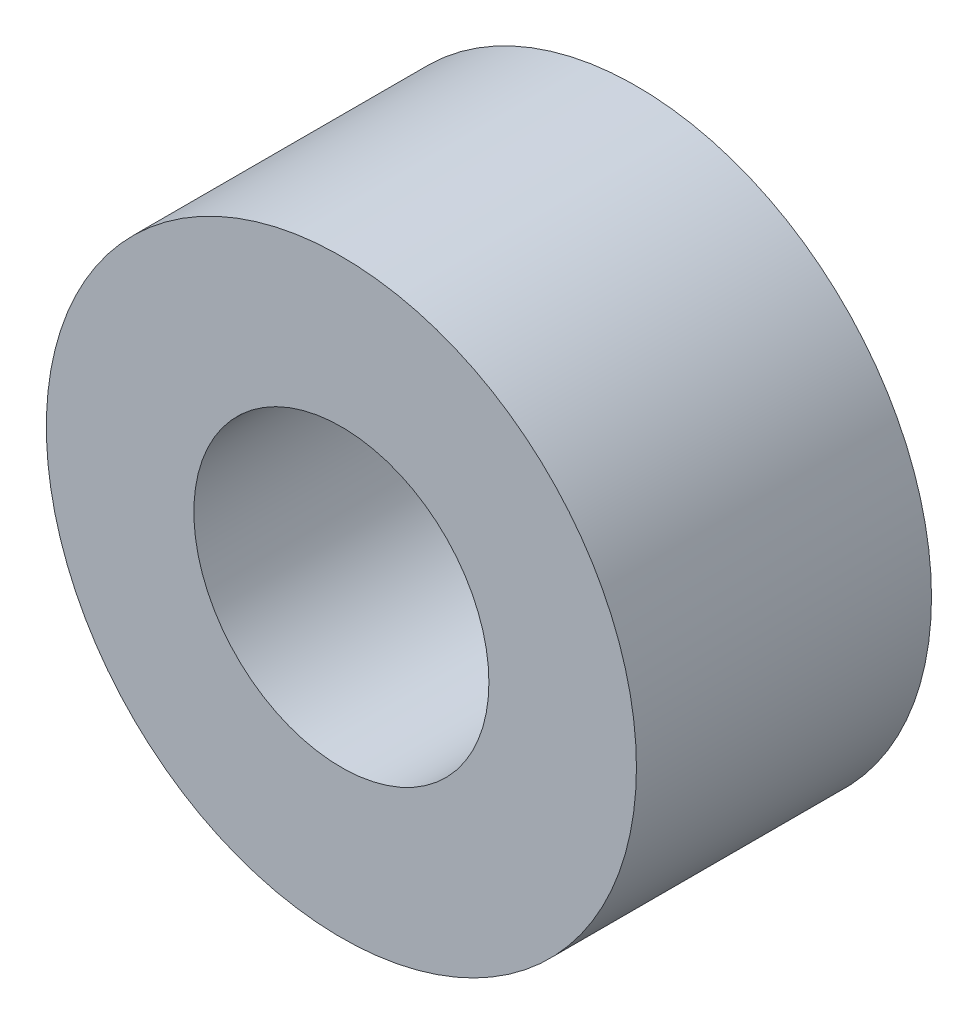
SolidWorks part; units mm, degrees
ref_plane "Front Plane" through (0, 0, 0) normal (0, 0, 1) x (1, 0, 0)
ref_plane "Top Plane" through (0, 0, 0) normal (0, 1, 0) x (1, 0, 0)
ref_plane "Right Plane" through (0, 0, 0) normal (1, 0, 0) x (0, 0, -1)
sketch "Sketch1" plane through (0, 0, 0) normal (0, 0, 1) x (1, 0, 0)
  circle A0 centre (0, 0) radius 3
  circle A1 centre (0, 0) radius 1.5
  dimension "D1" = 3
  dimension "D2" = 6
extrude "Boss-Extrude1" add sketch "Sketch1" along normal blind 3
